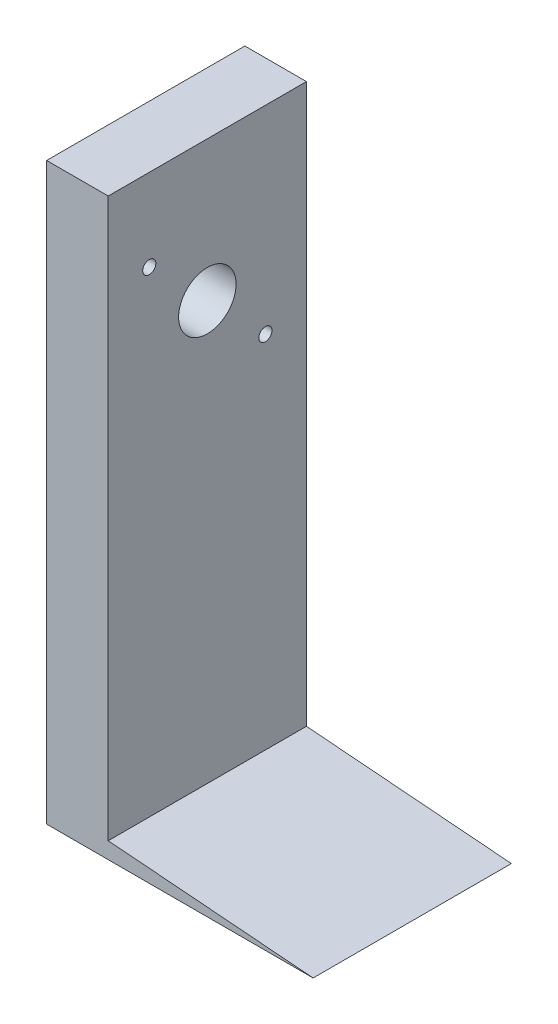
SolidWorks part; units mm, degrees
ref_plane "Front Plane" through (0, 0, 0) normal (0, 0, 1) x (1, 0, 0)
ref_plane "Top Plane" through (0, 0, 0) normal (0, 1, 0) x (1, 0, 0)
ref_plane "Right Plane" through (0, 0, 0) normal (1, 0, 0) x (0, 0, -1)
sketch "Sketch1" plane through (0, 0, 0) normal (1, 0, 0) x (0, 0, -1)
  line L0 (-17.9605, 63.5) -> (0, 45.5395) construction
  line L1 (-30.6605, -88.9) -> (30.6605, -88.9)
  line L2 (-30.6605, -88.9) -> (-30.6605, 88.9)
  line L3 (-30.6605, 88.9) -> (30.6605, 88.9)
  line L4 (30.6605, -88.9) -> (30.6605, 88.9)
  line L5 (0, 88.9) -> (0, -88.9) construction
  line L6 (-30.6605, 0) -> (30.6605, 0) construction
  line L7 (0, 45.5395) -> (17.9605, 27.579) construction
  circle A0 centre (0, 45.5395) radius 8.89
  circle A1 centre (-17.9605, 63.5) radius 2.032
  circle A2 centre (17.9605, 27.579) radius 2.032
  point P0 (0, 0)
  dimension "D3" = 17.78
  dimension "D4" = 25.4
  dimension "D5" = 12.7
  dimension "D6" = 25.4
  dimension "D7" = 4.064
  dimension "D1" = 177.8
  dimension "D2" = 45
extrude "Boss-Extrude1" add sketch "Sketch1" along normal blind 19.05
sketch "Sketch2" plane through (0, 0, 30.6605) normal (0, 0, 1) x (1, 0, 0)
  line L0 (19.05, -88.9) -> (82.4354, -88.9)
  line L1 (82.4354, -88.9) -> (19.05, -83.82)
  line L2 (19.05, -88.9) -> (19.05, 88.9) construction
  line L3 (19.05, -83.82) -> (19.05, -88.9)
  dimension "D1" = 5.08
extrude "Boss-Extrude2" add sketch "Sketch2" against normal up to surface (61.321 mm away) up to face at (9.525, 0, -30.6605)
equation "\"height\"=3.49339"
